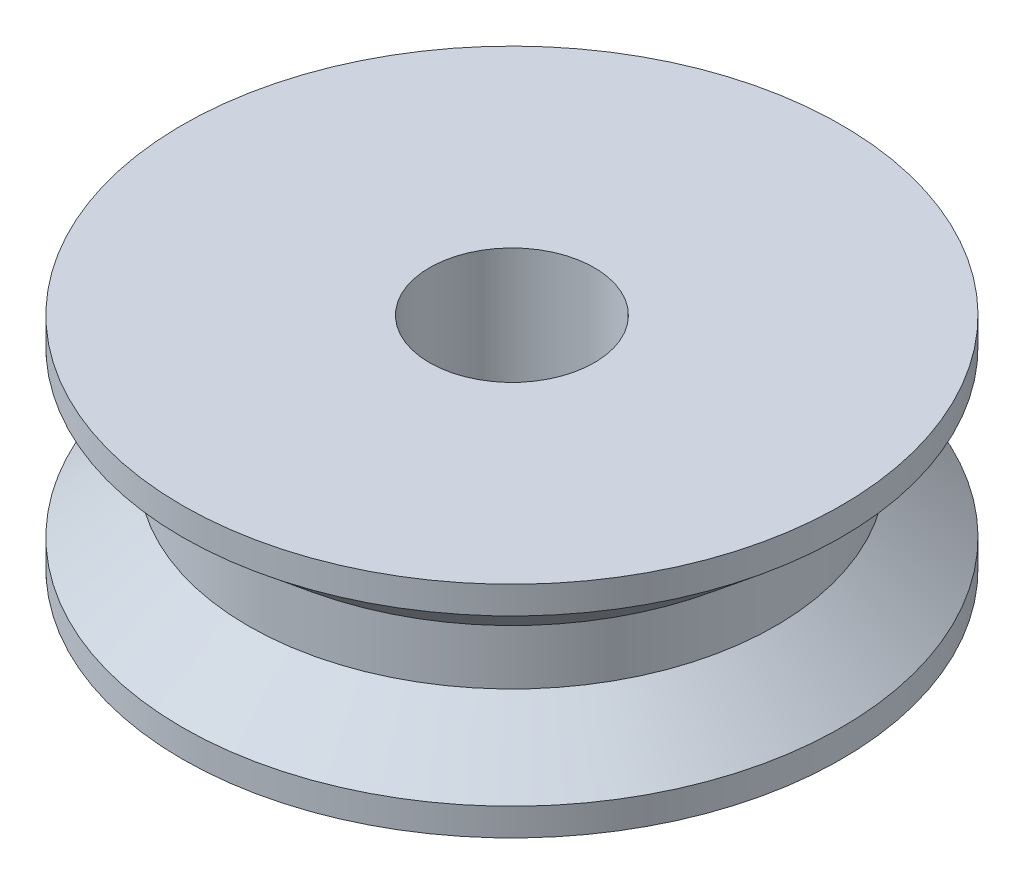
SolidWorks part; units mm, degrees
ref_plane "Front Plane" through (0, 0, 0) normal (0, 0, 1) x (1, 0, 0)
ref_plane "Top Plane" through (0, 0, 0) normal (0, 1, 0) x (1, 0, 0)
ref_plane "Right Plane" through (0, 0, 0) normal (1, 0, 0) x (0, 0, -1)
sketch "Sketch1" plane through (0, 0, 0) normal (0, 1, 0) x (1, 0, 0)
  circle A0 centre (0, 0) radius 6
  circle A1 centre (0, 0) radius 1.5
  dimension "D1" = 3
  dimension "D2" = 12
extrude "Boss-Extrude1" add sketch "Sketch1" along normal blind 4
sketch "Sketch6" plane through (0, 0, 0) normal (0, 0, 1) x (1, 0, 0)
  line L4 (6, 0.5) -> (6, 3.5)
  line L6 (4.8, 2.5) -> (4.8, 1.5)
  line L7 (4.8, 2.5) -> (6, 3.5)
  line L8 (4.8, 1.5) -> (6, 0.5)
  dimension "D1" = 4.8
  dimension "D2" = 6
  dimension "D3" = 0.5
  dimension "D4" = 1.5
  dimension "D5" = 2.5
revolve "Cut-Revolve1" cut sketch "Sketch6" angle 360 about axis through (0, 4, 0) along (0, -1, 0)
